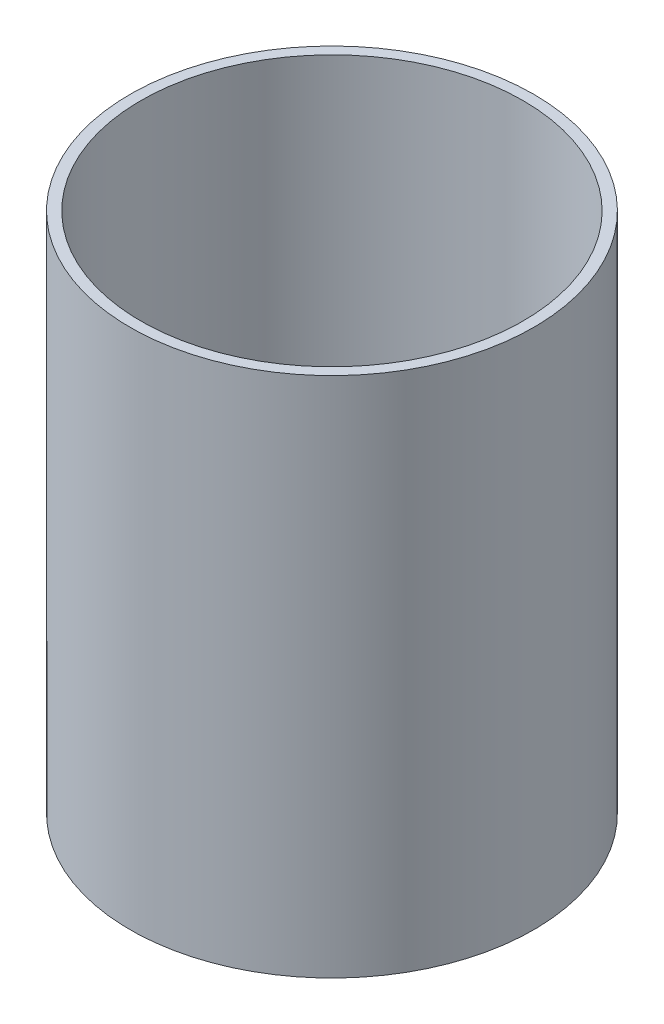
SolidWorks part; units mm, degrees
ref_plane "Front Plane" through (0, 0, 0) normal (0, 0, 1) x (1, 0, 0)
ref_plane "Top Plane" through (0, 0, 0) normal (0, 1, 0) x (1, 0, 0)
ref_plane "Right Plane" through (0, 0, 0) normal (1, 0, 0) x (0, 0, -1)
sketch "Sketch1" plane through (0, 0, 0) normal (0, 0, 1) x (1, 0, 0)
  line L1 (26.9748, 0) -> (28.4988, 0)
  line L2 (26.9748, 0) -> (26.9748, 73.66)
  line L3 (26.9748, 73.66) -> (28.4988, 73.66)
  line L4 (28.4988, 0) -> (28.4988, 73.66)
  dimension "D1" = 28.4988
  dimension "D2" = 1.524
  dimension "D3" = 73.66
  dimension "D4" = 0
ref_axis "Axis1" through (0, -13.97, 0) along (0, 1, 0)
revolve "Revolve1" add sketch "Sketch1" angle 360 about axis through (0, -13.97, 0) along (0, 1, 0)
